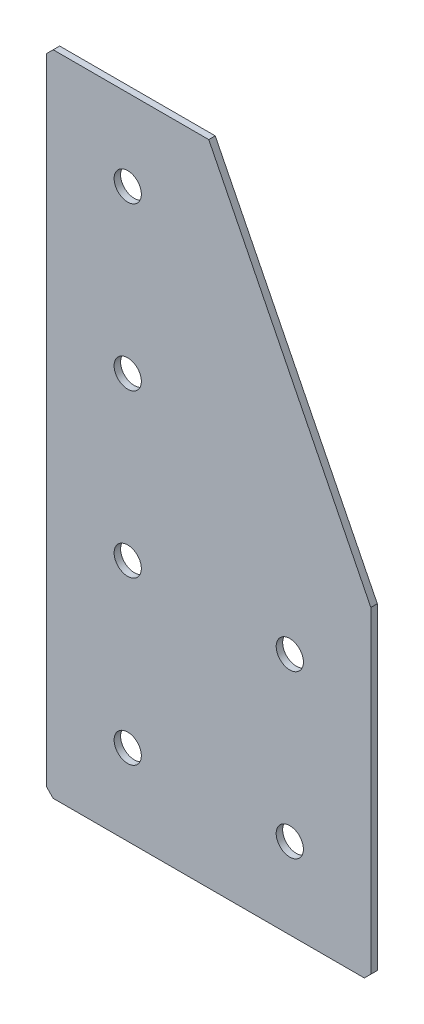
SolidWorks part; units mm, degrees
material "Простая углеродистая сталь"
ref_plane "Спереди(Плоскость XY)" through (0, 0, 0) normal (0, 0, 1) x (1, 0, 0)
ref_plane "Сверху(Плоскость XZ)" through (0, 0, 0) normal (0, 1, 0) x (1, 0, 0)
ref_plane "Справа(Плоскость ZY)" through (0, 0, 0) normal (1, 0, 0) x (0, 0, -1)
sketch "Эскиз1" plane through (0, 0, 0) normal (0, 0, -1) x (1, 0, 0)
  line L0 (0, 0) -> (0, 200)
  line L1 (0, 200) -> (100, 200)
  line L2 (100, 200) -> (100, 100)
  line L3 (100, 100) -> (50, 100) construction
  line L4 (50, 100) -> (50, 0) construction
  line L5 (50, 0) -> (0, 0)
  line L6 (100, 100) -> (50, 0)
  dimension "D1" = 200
  dimension "D2" = 100
  dimension "D3" = 50
  dimension "D4" = 50
extrude "Бобышка-Вытянуть1" add sketch "Эскиз1" along normal blind 2
hole_wizard "Отверстие с зазором M81" positions "Эскиз2" profile "Эскиз3" hole size "M8" standard "DIN" end condition up to next
sketch "Эскиз2" plane through (0, 0, -2) normal (0, 0, -1) x (1, 0, 0)
  line L0 (25, 0) -> (25, 200) construction
  line L1 (0, 0) -> (50, 0) construction
  line L2 (100, 200) -> (0, 200) construction
  point P0 (25, 175)
  point P2 (25, 125)
  point P4 (25, 75)
  point P6 (25, 25)
  point P27 (75, 175)
  point P29 (75, 125)
  dimension "D1" = 50
  dimension "D2" = 50
  dimension "D3" = 50
  dimension "D4" = 25
  dimension "D5" = 50
sketch "Эскиз3" plane through (25, -175, -2) normal (1, 0, 0) x (0, 1, 0)
  line L0 (0, 0) -> (0, 2)
  line L1 (0, 2) -> (4.2, 2)
  line L2 (4.2, 2) -> (4.2, 0)
  line L5 (4.2, 0) -> (0, 0)
  line L11 (0, -6.35) -> (0, 107.95) construction
  dimension "Диаметр сквозного отверстия" = 8.4
  dimension "Глубина сквозного отверстия" = 2
chamfer "Фаска1" distance 2 angle 45 3 edges at (0, 0, -1) (100, -200, -1) (0, -200, -1)
